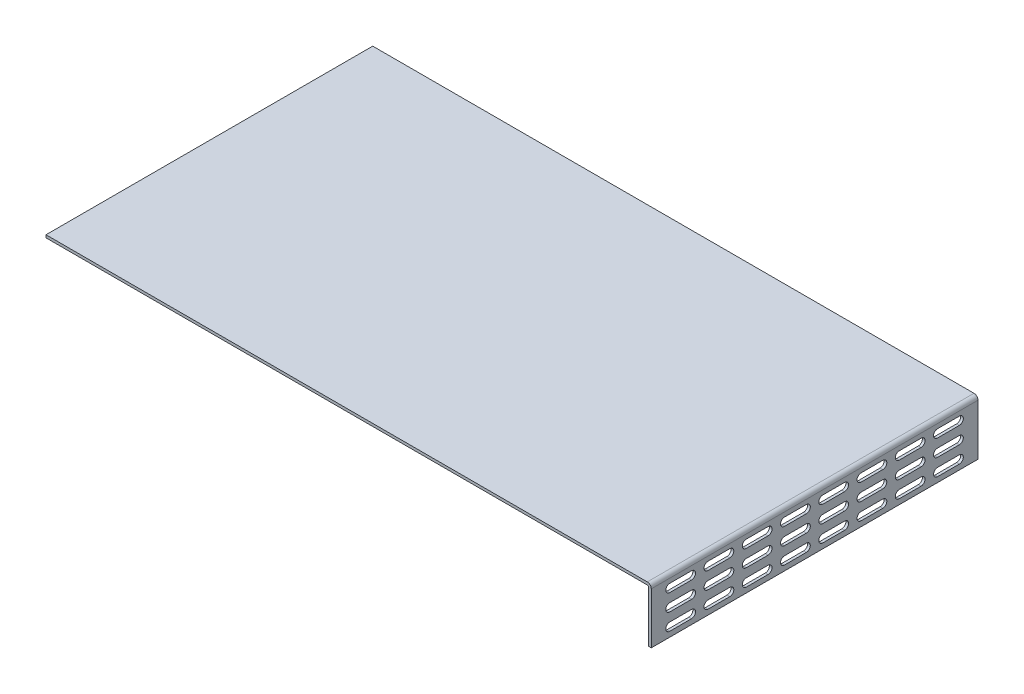
SolidWorks part; units mm, degrees
ref_plane "Front Plane" through (0, 0, 0) normal (0, 0, 1) x (1, 0, 0)
ref_plane "Top Plane" through (0, 0, 0) normal (0, 1, 0) x (1, 0, 0)
ref_plane "Right Plane" through (0, 0, 0) normal (1, 0, 0) x (0, 0, -1)
sketch "Sketch1" plane through (0, 0, 0) normal (0, 0, 1) x (1, 0, 0)
  line L0 (0, 0) -> (0, 20.32)
  line L1 (0, 20.32) -> (-223.0437, 20.32)
  line L2 (-0.9906, 0) -> (-0.9906, 19.3294)
  line L3 (-0.9906, 19.3294) -> (-223.0437, 19.3294)
  line L4 (-223.0437, 20.32) -> (-223.0437, 19.3294)
  line L5 (-0.9906, 0) -> (0, 0)
  dimension "D1" = 223.0437
  dimension "D2" = 20.32
extrude "Boss-Extrude1" add sketch "Sketch1" along normal mid plane 120.396
fillet "Fillet1" radius 0.4826 1 edges at (-0.9906, 19.3294, 0)
fillet "Fillet2" radius 1.4732 1 edges at (0, 20.32, 0)
sketch "Sketch2" plane through (0, 0, 0) normal (1, 0, 0) x (0, 0, -1)
  line L0 (-53.3908, 3.3782) -> (-45.3644, 3.3782) construction
  line L1 (-53.3908, 4.8514) -> (-45.3644, 4.8514)
  line L2 (-53.3908, 1.905) -> (-45.3644, 1.905)
  line L3 (-60.198, 0) -> (-60.198, 18.8468) construction
  line L4 (-60.198, 0) -> (60.198, 0) construction
  arc A0 (-53.3908, 4.8514) -> (-53.3908, 1.905) centre (-53.3908, 3.3782) ccw
  arc A1 (-45.3644, 1.905) -> (-45.3644, 4.8514) centre (-45.3644, 3.3782) ccw
  point P2 (-49.3776, 3.3782)
  dimension "D3" = 6.8072
  dimension "D1" = 8.0264
  dimension "D2" = 2.9464
  dimension "D4" = 1.905
extrude "Cut-Extrude1" cut sketch "Sketch2" against normal up to surface (0.9906 mm away) up to face at (-0.9906, 9.4234, 0)
pattern_linear "LPattern1" count 3 spacing 6.1722 along (0, 1, 0) count 8 spacing 14.097 along (0, 0, -1) of "Cut-Extrude1"
